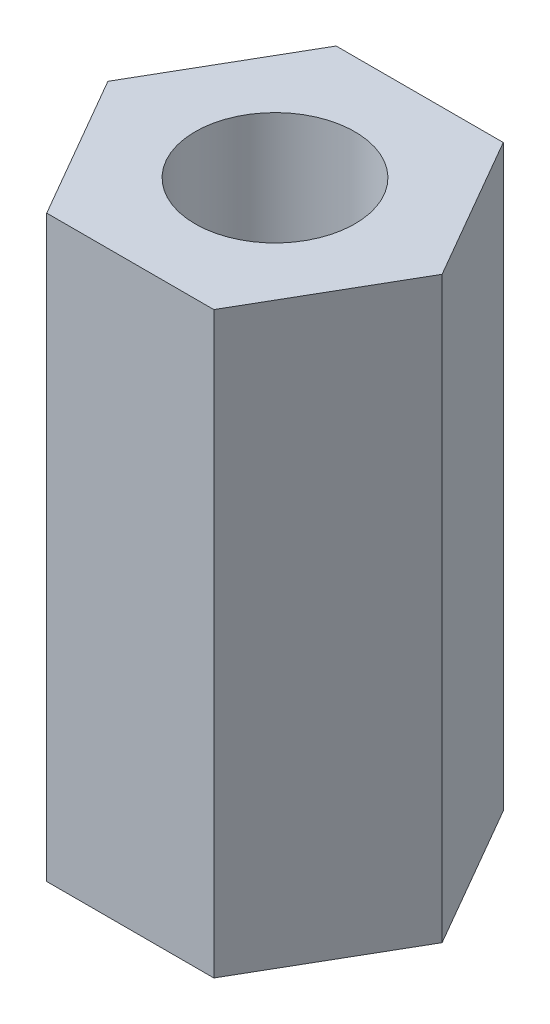
SolidWorks part; units mm, degrees
ref_plane "Front Plane" through (0, 0, 0) normal (0, 0, 1) x (1, 0, 0)
ref_plane "Top Plane" through (0, 0, 0) normal (0, 1, 0) x (1, 0, 0)
ref_plane "Right Plane" through (0, 0, 0) normal (1, 0, 0) x (0, 0, -1)
sketch "Sketch1" plane through (0, 0, 0) normal (0, 1, 0) x (1, 0, 0)
  line L0 (-1.8331, 3.175) -> (-1.8331, -3.175) construction
  line L17 (3.6662, 0) -> (1.8331, 3.175)
  line L18 (1.8331, 3.175) -> (-1.8331, 3.175)
  line L19 (-1.8331, 3.175) -> (-3.6662, 0)
  line L20 (-3.6662, 0) -> (-1.8331, -3.175)
  line L21 (-1.8331, -3.175) -> (1.8331, -3.175)
  line L22 (1.8331, -3.175) -> (3.6662, 0)
  circle A0 centre (0, 0) radius 1.7526
  circle A1 centre (0, 0) radius 3.6662 construction
extrude "Boss-Extrude1" add sketch "Sketch1" along normal blind 12.7
